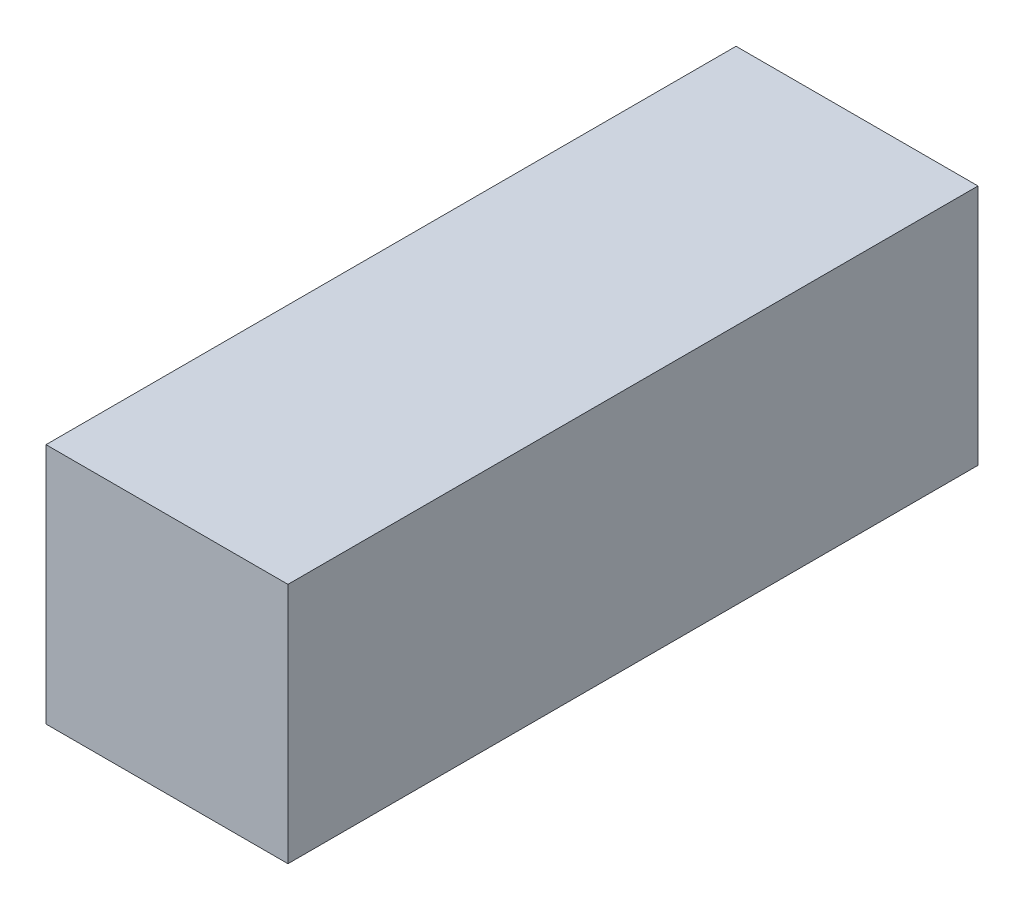
SolidWorks part; units mm, degrees
ref_plane "Ön Düzlem" through (0, 0, 0) normal (0, 0, 1) x (1, 0, 0)
ref_plane "Üst Düzlem" through (0, 0, 0) normal (0, 1, 0) x (1, 0, 0)
ref_plane "Sağ Düzlem" through (0, 0, 0) normal (1, 0, 0) x (0, 0, -1)
sketch "Sketch2" plane through (0, 0, 0) normal (1, 0, 0) x (0, 0, -1)
  line L1 (3.85, -1.35) -> (-3.85, -1.35)
  line L2 (3.85, -1.35) -> (3.85, 1.35)
  line L3 (3.85, 1.35) -> (-3.85, 1.35)
  line L4 (-3.85, -1.35) -> (-3.85, 1.35)
  line L5 (3.85, -1.35) -> (-3.85, 1.35) construction
  line L6 (3.85, 1.35) -> (-3.85, -1.35) construction
  point P0 (0, 0)
  dimension "D1" = 7.7
  dimension "D2" = 2.7
extrude "Boss-Extrude3" add sketch "Sketch2" along normal blind 2.7
